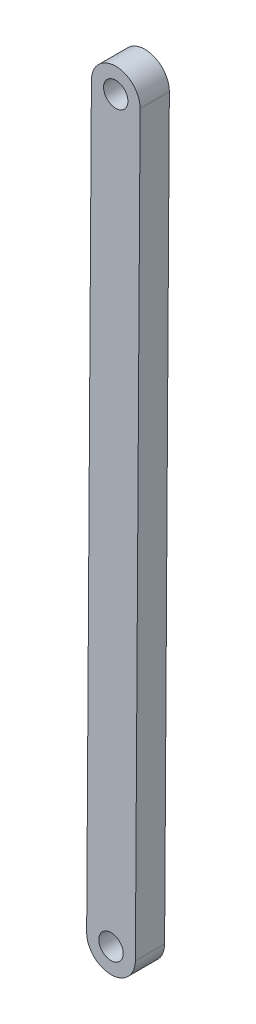
SolidWorks part; units mm, degrees
ref_plane "Front Plane" through (0, 0, 0) normal (0, 0, 1) x (1, 0, 0)
ref_plane "Top Plane" through (0, 0, 0) normal (0, 1, 0) x (1, 0, 0)
ref_plane "Right Plane" through (0, 0, 0) normal (1, 0, 0) x (0, 0, -1)
sketch "Sketch1" plane through (0, 0, 0) normal (0, 0, 1) x (1, 0, 0)
  line L0 (0, 0) -> (-1.9492, -304) construction
  line L1 (9.9998, -0.0641) -> (8.0506, -304.0641)
  line L2 (-9.9998, 0.0641) -> (-11.949, -303.9359)
  arc A0 (9.9998, -0.0641) -> (-9.9998, 0.0641) centre (0, 0) ccw
  arc A1 (-11.949, -303.9359) -> (8.0506, -304.0641) centre (-1.9492, -304) ccw
  circle A2 centre (-1.9492, -304) radius 5
  circle A3 centre (0, 0) radius 5
  point P3 (-0.9746, -152)
  dimension "D3" = 10
  dimension "D4" = 10
  dimension "D1" = 304
  dimension "D2" = 20
extrude "Boss-Extrude1" add sketch "Sketch1" along normal blind 12
